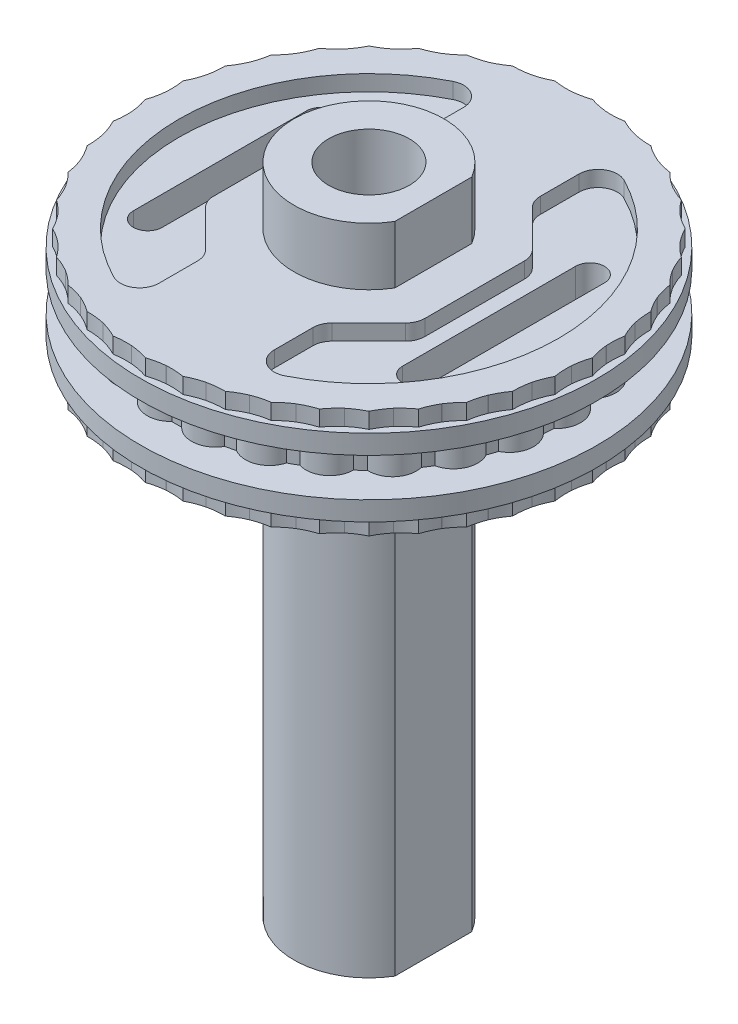
SolidWorks part; units mm, degrees
ref_plane "Front Plane" through (0, 0, 0) normal (0, 0, 1) x (1, 0, 0)
ref_plane "Top Plane" through (0, 0, 0) normal (0, 1, 0) x (1, 0, 0)
ref_plane "Right Plane" through (0, 0, 0) normal (1, 0, 0) x (0, 0, -1)
sketch "Sketch1" plane through (0, 0, 0) normal (1, 0, 0) x (0, 0, -1)
  line L0 (0, -0.599) -> (0, 0.599) construction
  line L1 (-5, -0.5) -> (0, -0.5)
  line L2 (-5, -0.5) -> (-5, 0.5)
  line L3 (-5, 0.5) -> (0, 0.5)
  line L4 (0, -0.5) -> (0, 0.5)
  line L5 (-5, -0.5) -> (0, 0.5) construction
  line L6 (-5, 0.5) -> (0, -0.5) construction
  point P0 (-2.5, 0)
  point P8 (0, 0)
  dimension "D2" = 5
  dimension "D3" = 1
revolve "Revolve1" add sketch "Sketch1" angle 360 about L0
sketch "Sketch2" plane through (0, 0.5, 0) normal (0, 1, 0) x (1, 0, 0)
  line L0 (0, 0) -> (0, 5.2249) construction
  arc A0 (-0.5, 4.9749) -> (0.5, 4.9749) centre (0, 4.5999) cw
  circle A1 centre (0, 0) radius 5 construction
  circle A4 centre (0, 0) radius 5
  arc A5 (0.5, 4.9749) -> (-0.5, 4.9749) centre (0, 0) ccw
  dimension "D1" = 0
  dimension "D2" = 1
  dimension "D3" = 0.25
extrude "Boss-Extrude1" add sketch "Sketch2" against normal up to surface (1 mm away) from surface at 0 up to face at (0, -0.5, -5) starting at face at (0, 0.5, -5)
pattern_circular "CirPattern1" count 25 over 360 about axis through (0, 0, 0) along (0, 1, 0) of "Boss-Extrude1"
sketch "Sketch3" plane through (0, 0, 0) normal (1, 0, 0) x (0, 0, -1)
  line L0 (0, 0) -> (0, 0.5) construction
  line L1 (0, 0.5) -> (-5.9387, 0.5)
  line L3 (-5.7387, 1) -> (-5.9387, 1)
  line L4 (-5.9387, 0.5) -> (-5.9387, 1)
  line L6 (0, 0.5) -> (0, 1.4)
  line L7 (0, 1.4) -> (-5.7387, 1.4)
  line L8 (-5.7387, 1) -> (-5.7387, 1.4)
  line L9 (0.8114, 0.5) -> (-0.1866, 0.5) construction
  line L10 (-5.1887, 0.5) -> (-5.1887, -0.5) construction
  dimension "D1" = 0.5
  dimension "D2" = 0.4
  dimension "D3" = 0.75
  dimension "D4" = 0.2
revolve "Revolve2" add sketch "Sketch3" angle 360 about L0
sketch "Sketch4" plane through (0, 1.4, 0) normal (0, 1, 0) x (1, 0, 0)
  line L0 (0, 0) -> (0, 5.8168) construction
  arc A0 (-0.5, 5.7168) -> (0, 5.8168) centre (-0.639, 7.712) ccw
  arc A1 (0, 5.8168) -> (0.5, 5.7168) centre (0.639, 7.712) ccw
  circle A3 centre (0, 0) radius 5.7387 construction
  circle A4 centre (0, 0) radius 5.7387
  arc A5 (0.5, 5.7168) -> (-0.5, 5.7168) centre (0, 0) ccw
  circle M2 centre (0, 0) radius 5.7387
  dimension "D4" = 2
  dimension "D2" = 0.1
  dimension "D3" = 1
  dimension "D1" = 0
extrude "Boss-Extrude2" add sketch "Sketch4" against normal up to surface (0.4 mm away) contours L0 A1 M2 | A5 L0 A0 up to face at (0, 1, -5.9387)
pattern_circular "CirPattern2" count 40 over 360 about axis through (0, 0, 0) along (0, 1, 0) of "Boss-Extrude2"
mirror "Mirror2" about plane through (0, 0, 0) normal (0, 1, 0) of "Revolve2", "Boss-Extrude2", "CirPattern2"
sketch "Sketch16" plane through (0, 1.4, 0) normal (0, 1, 0) x (1, 0, 0)
  line L80 (-1.3373, 5.5807) -> (-1.3421, 5.5795)
  line L81 (-2.1938, 5.3028) -> (-2.1984, 5.3009)
  line L82 (-2.9963, 4.8943) -> (-3.0006, 4.8917)
  line L83 (-3.7251, 4.3653) -> (-3.7289, 4.3621)
  line L84 (-4.3621, 3.7289) -> (-4.3653, 3.7251)
  line L85 (-4.8917, 3.0006) -> (-4.8943, 2.9963)
  line L86 (-5.3009, 2.1984) -> (-5.3028, 2.1938)
  line L87 (-5.5795, 1.3421) -> (-5.5807, 1.3373)
  line L88 (-5.7208, 0.4527) -> (-5.7212, 0.4478)
  line L89 (-5.7212, -0.4478) -> (-5.7208, -0.4527)
  line L90 (-5.5807, -1.3373) -> (-5.5795, -1.3421)
  line L91 (-5.3028, -2.1938) -> (-5.3009, -2.1984)
  line L92 (-4.8943, -2.9963) -> (-4.8917, -3.0006)
  line L93 (-4.3653, -3.7251) -> (-4.3621, -3.7289)
  line L94 (-3.7289, -4.3621) -> (-3.7251, -4.3653)
  line L95 (-3.0006, -4.8917) -> (-2.9963, -4.8943)
  line L96 (-2.1984, -5.3009) -> (-2.1938, -5.3028)
  line L97 (-1.3421, -5.5795) -> (-1.3373, -5.5807)
  line L98 (-0.4527, -5.7208) -> (-0.4478, -5.7212)
  line L99 (0.4478, -5.7212) -> (0.4527, -5.7208)
  line L100 (1.3373, -5.5807) -> (1.3421, -5.5795)
  line L101 (2.1938, -5.3028) -> (2.1984, -5.3009)
  line L102 (2.9963, -4.8943) -> (3.0006, -4.8917)
  line L103 (3.7251, -4.3653) -> (3.7289, -4.3621)
  line L104 (4.3621, -3.7289) -> (4.3653, -3.7251)
  line L105 (4.8917, -3.0006) -> (4.8943, -2.9963)
  line L106 (5.3009, -2.1984) -> (5.3028, -2.1938)
  line L107 (5.5795, -1.3421) -> (5.5807, -1.3373)
  line L108 (5.7208, -0.4527) -> (5.7212, -0.4478)
  line L109 (5.7212, 0.4478) -> (5.7208, 0.4527)
  line L110 (5.5807, 1.3373) -> (5.5795, 1.3421)
  line L111 (5.3028, 2.1938) -> (5.3009, 2.1984)
  line L112 (4.8943, 2.9963) -> (4.8917, 3.0006)
  line L113 (4.3653, 3.7251) -> (4.3621, 3.7289)
  line L114 (3.7289, 4.3621) -> (3.7251, 4.3653)
  line L115 (3.0006, 4.8917) -> (2.9963, 4.8943)
  line L116 (2.1984, 5.3009) -> (2.1938, 5.3028)
  line L117 (1.3421, 5.5795) -> (1.3373, 5.5807)
  line L118 (0.4527, 5.7208) -> (0.4478, 5.7212)
  line L119 (-0.4478, 5.7212) -> (-0.4527, 5.7208)
  line L120 (-1.3373, 5.5807) -> (-1.3421, 5.5795)
  line L121 (-2.1938, 5.3028) -> (-2.1984, 5.3009)
  line L122 (-2.9963, 4.8943) -> (-3.0006, 4.8917)
  line L123 (-3.7251, 4.3653) -> (-3.7289, 4.3621)
  line L124 (-4.3621, 3.7289) -> (-4.3653, 3.7251)
  line L125 (-4.8917, 3.0006) -> (-4.8943, 2.9963)
  line L126 (-5.3009, 2.1984) -> (-5.3028, 2.1938)
  line L127 (-5.5795, 1.3421) -> (-5.5807, 1.3373)
  line L128 (-5.7208, 0.4527) -> (-5.7212, 0.4478)
  line L129 (-5.7212, -0.4478) -> (-5.7208, -0.4527)
  line L130 (-5.5807, -1.3373) -> (-5.5795, -1.3421)
  line L131 (-5.3028, -2.1938) -> (-5.3009, -2.1984)
  line L132 (-4.8943, -2.9963) -> (-4.8917, -3.0006)
  line L133 (-4.3653, -3.7251) -> (-4.3621, -3.7289)
  line L134 (-3.7289, -4.3621) -> (-3.7251, -4.3653)
  line L135 (-3.0006, -4.8917) -> (-2.9963, -4.8943)
  line L136 (-2.1984, -5.3009) -> (-2.1938, -5.3028)
  line L137 (-1.3421, -5.5795) -> (-1.3373, -5.5807)
  line L138 (-0.4527, -5.7208) -> (-0.4478, -5.7212)
  line L139 (0.4478, -5.7212) -> (0.4527, -5.7208)
  line L140 (1.3373, -5.5807) -> (1.3421, -5.5795)
  line L141 (2.1938, -5.3028) -> (2.1984, -5.3009)
  line L142 (2.9963, -4.8943) -> (3.0006, -4.8917)
  line L143 (3.7251, -4.3653) -> (3.7289, -4.3621)
  line L144 (4.3621, -3.7289) -> (4.3653, -3.7251)
  line L145 (4.8917, -3.0006) -> (4.8943, -2.9963)
  line L146 (5.3009, -2.1984) -> (5.3028, -2.1938)
  line L147 (5.5795, -1.3421) -> (5.5807, -1.3373)
  line L148 (5.7208, -0.4527) -> (5.7212, -0.4478)
  line L149 (5.7212, 0.4478) -> (5.7208, 0.4527)
  line L150 (5.5807, 1.3373) -> (5.5795, 1.3421)
  line L151 (5.3028, 2.1938) -> (5.3009, 2.1984)
  line L152 (4.8943, 2.9963) -> (4.8917, 3.0006)
  line L153 (4.3653, 3.7251) -> (4.3621, 3.7289)
  line L154 (3.7289, 4.3621) -> (3.7251, 4.3653)
  line L155 (3.0006, 4.8917) -> (2.9963, 4.8943)
  line L156 (2.1984, 5.3009) -> (2.1938, 5.3028)
  line L157 (1.3421, 5.5795) -> (1.3373, 5.5807)
  line L158 (0.4527, 5.7208) -> (0.4478, 5.7212)
  line L159 (-0.4478, 5.7212) -> (-0.4527, 5.7208)
  arc A160 (-1.7975, 5.5321) -> (-1.3421, 5.5795) centre (-1.7754, 7.532) ccw
  arc A161 (-2.1938, 5.3028) -> (-1.7975, 5.5321) centre (-2.9909, 7.1371) ccw
  arc A162 (-2.6408, 5.1828) -> (-2.1984, 5.3009) centre (-2.9318, 7.1616) ccw
  arc A163 (-2.9963, 4.8943) -> (-2.6408, 5.1828) centre (-4.0706, 6.5813) ccw
  arc A164 (-3.4191, 4.7059) -> (-3.0006, 4.8917) centre (-4.016, 6.6148) ccw
  arc A165 (-3.7251, 4.3653) -> (-3.4191, 4.7059) centre (-5.05, 5.8635) ccw
  arc A166 (-4.1131, 4.1131) -> (-3.7289, 4.3621) centre (-5.0013, 5.9051) ccw
  arc A167 (-4.3621, 3.7289) -> (-4.1131, 4.1131) centre (-5.9051, 5.0013) ccw
  arc A168 (-4.7059, 3.4191) -> (-4.3653, 3.7251) centre (-5.8635, 5.05) ccw
  arc A169 (-4.8917, 3.0006) -> (-4.7059, 3.4191) centre (-6.6148, 4.016) ccw
  arc A170 (-5.1828, 2.6408) -> (-4.8943, 2.9963) centre (-6.5813, 4.0706) ccw
  arc A171 (-5.3009, 2.1984) -> (-5.1828, 2.6408) centre (-7.1616, 2.9318) ccw
  arc A172 (-5.5321, 1.7975) -> (-5.3028, 2.1938) centre (-7.1371, 2.9909) ccw
  arc A173 (-5.5795, 1.3421) -> (-5.5321, 1.7975) centre (-7.532, 1.7754) ccw
  arc A174 (-5.7452, 0.91) -> (-5.5807, 1.3373) centre (-7.5171, 1.8376) ccw
  arc A175 (-5.7208, 0.4527) -> (-5.7452, 0.91) centre (-7.717, 0.5753) ccw
  arc A176 (-5.8168, 0) -> (-5.7212, 0.4478) centre (-7.712, 0.639) ccw
  arc A177 (-5.7212, -0.4478) -> (-5.8168, 0) centre (-7.712, -0.639) ccw
  arc A178 (-5.7452, -0.91) -> (-5.7208, -0.4527) centre (-7.717, -0.5753) ccw
  arc A179 (-5.5807, -1.3373) -> (-5.7452, -0.91) centre (-7.5171, -1.8376) ccw
  arc A180 (-5.5321, -1.7975) -> (-5.5795, -1.3421) centre (-7.532, -1.7754) ccw
  arc A181 (-5.3028, -2.1938) -> (-5.5321, -1.7975) centre (-7.1371, -2.9909) ccw
  arc A182 (-5.1828, -2.6408) -> (-5.3009, -2.1984) centre (-7.1616, -2.9318) ccw
  arc A183 (-4.8943, -2.9963) -> (-5.1828, -2.6408) centre (-6.5813, -4.0706) ccw
  arc A184 (-4.7059, -3.4191) -> (-4.8917, -3.0006) centre (-6.6148, -4.016) ccw
  arc A185 (-4.3653, -3.7251) -> (-4.7059, -3.4191) centre (-5.8635, -5.05) ccw
  arc A186 (-4.1131, -4.1131) -> (-4.3621, -3.7289) centre (-5.9051, -5.0013) ccw
  arc A187 (-3.7289, -4.3621) -> (-4.1131, -4.1131) centre (-5.0013, -5.9051) ccw
  arc A188 (-3.4191, -4.7059) -> (-3.7251, -4.3653) centre (-5.05, -5.8635) ccw
  arc A189 (-3.0006, -4.8917) -> (-3.4191, -4.7059) centre (-4.016, -6.6148) ccw
  arc A190 (-2.6408, -5.1828) -> (-2.9963, -4.8943) centre (-4.0706, -6.5813) ccw
  arc A191 (-2.1984, -5.3009) -> (-2.6408, -5.1828) centre (-2.9318, -7.1616) ccw
  arc A192 (-1.7975, -5.5321) -> (-2.1938, -5.3028) centre (-2.9909, -7.1371) ccw
  arc A193 (-1.3421, -5.5795) -> (-1.7975, -5.5321) centre (-1.7754, -7.532) ccw
  arc A194 (-0.91, -5.7452) -> (-1.3373, -5.5807) centre (-1.8376, -7.5171) ccw
  arc A195 (-0.4527, -5.7208) -> (-0.91, -5.7452) centre (-0.5753, -7.717) ccw
  arc A196 (0, -5.8168) -> (-0.4478, -5.7212) centre (-0.639, -7.712) ccw
  arc A197 (0.4478, -5.7212) -> (0, -5.8168) centre (0.639, -7.712) ccw
  arc A198 (0.91, -5.7452) -> (0.4527, -5.7208) centre (0.5753, -7.717) ccw
  arc A199 (1.3373, -5.5807) -> (0.91, -5.7452) centre (1.8376, -7.5171) ccw
  arc A200 (1.7975, -5.5321) -> (1.3421, -5.5795) centre (1.7754, -7.532) ccw
  arc A201 (2.1938, -5.3028) -> (1.7975, -5.5321) centre (2.9909, -7.1371) ccw
  arc A202 (2.6408, -5.1828) -> (2.1984, -5.3009) centre (2.9318, -7.1616) ccw
  arc A203 (2.9963, -4.8943) -> (2.6408, -5.1828) centre (4.0706, -6.5813) ccw
  arc A204 (3.4191, -4.7059) -> (3.0006, -4.8917) centre (4.016, -6.6148) ccw
  arc A205 (3.7251, -4.3653) -> (3.4191, -4.7059) centre (5.05, -5.8635) ccw
  arc A206 (4.1131, -4.1131) -> (3.7289, -4.3621) centre (5.0013, -5.9051) ccw
  arc A207 (4.3621, -3.7289) -> (4.1131, -4.1131) centre (5.9051, -5.0013) ccw
  arc A208 (4.7059, -3.4191) -> (4.3653, -3.7251) centre (5.8635, -5.05) ccw
  arc A209 (4.8917, -3.0006) -> (4.7059, -3.4191) centre (6.6148, -4.016) ccw
  arc A210 (5.1828, -2.6408) -> (4.8943, -2.9963) centre (6.5813, -4.0706) ccw
  arc A211 (5.3009, -2.1984) -> (5.1828, -2.6408) centre (7.1616, -2.9318) ccw
  arc A212 (5.5321, -1.7975) -> (5.3028, -2.1938) centre (7.1371, -2.9909) ccw
  arc A213 (5.5795, -1.3421) -> (5.5321, -1.7975) centre (7.532, -1.7754) ccw
  arc A214 (5.7452, -0.91) -> (5.5807, -1.3373) centre (7.5171, -1.8376) ccw
  arc A215 (5.7208, -0.4527) -> (5.7452, -0.91) centre (7.717, -0.5753) ccw
  arc A216 (5.8168, 0) -> (5.7212, -0.4478) centre (7.712, -0.639) ccw
  arc A217 (5.7212, 0.4478) -> (5.8168, 0) centre (7.712, 0.639) ccw
  arc A218 (5.7452, 0.91) -> (5.7208, 0.4527) centre (7.717, 0.5753) ccw
  arc A219 (5.5807, 1.3373) -> (5.7452, 0.91) centre (7.5171, 1.8376) ccw
  arc A220 (5.5321, 1.7975) -> (5.5795, 1.3421) centre (7.532, 1.7754) ccw
  arc A221 (5.3028, 2.1938) -> (5.5321, 1.7975) centre (7.1371, 2.9909) ccw
  arc A222 (5.1828, 2.6408) -> (5.3009, 2.1984) centre (7.1616, 2.9318) ccw
  arc A223 (4.8943, 2.9963) -> (5.1828, 2.6408) centre (6.5813, 4.0706) ccw
  arc A224 (4.7059, 3.4191) -> (4.8917, 3.0006) centre (6.6148, 4.016) ccw
  arc A225 (4.3653, 3.7251) -> (4.7059, 3.4191) centre (5.8635, 5.05) ccw
  arc A226 (4.1131, 4.1131) -> (4.3621, 3.7289) centre (5.9051, 5.0013) ccw
  arc A227 (3.7289, 4.3621) -> (4.1131, 4.1131) centre (5.0013, 5.9051) ccw
  arc A228 (3.4191, 4.7059) -> (3.7251, 4.3653) centre (5.05, 5.8635) ccw
  arc A229 (3.0006, 4.8917) -> (3.4191, 4.7059) centre (4.016, 6.6148) ccw
  arc A230 (2.6408, 5.1828) -> (2.9963, 4.8943) centre (4.0706, 6.5813) ccw
  arc A231 (2.1984, 5.3009) -> (2.6408, 5.1828) centre (2.9318, 7.1616) ccw
  arc A232 (1.7975, 5.5321) -> (2.1938, 5.3028) centre (2.9909, 7.1371) ccw
  arc A233 (1.3421, 5.5795) -> (1.7975, 5.5321) centre (1.7754, 7.532) ccw
  arc A234 (0.91, 5.7452) -> (1.3373, 5.5807) centre (1.8376, 7.5171) ccw
  arc A235 (0.4527, 5.7208) -> (0.91, 5.7452) centre (0.5753, 7.717) ccw
  arc A236 (0, 5.8168) -> (0.4478, 5.7212) centre (0.639, 7.712) ccw
  arc A237 (-0.4478, 5.7212) -> (0, 5.8168) centre (-0.639, 7.712) ccw
  arc A238 (-0.91, 5.7452) -> (-0.4527, 5.7208) centre (-0.5753, 7.717) ccw
  arc A239 (-1.3373, 5.5807) -> (-0.91, 5.7452) centre (-1.8376, 7.5171) ccw
  arc A240 (-1.7975, 5.5321) -> (-1.3421, 5.5795) centre (-1.7754, 7.532) ccw
  arc A241 (-2.1938, 5.3028) -> (-1.7975, 5.5321) centre (-2.9909, 7.1371) ccw
  arc A242 (-2.6408, 5.1828) -> (-2.1984, 5.3009) centre (-2.9318, 7.1616) ccw
  arc A243 (-2.9963, 4.8943) -> (-2.6408, 5.1828) centre (-4.0706, 6.5813) ccw
  arc A244 (-3.4191, 4.7059) -> (-3.0006, 4.8917) centre (-4.016, 6.6148) ccw
  arc A245 (-3.7251, 4.3653) -> (-3.4191, 4.7059) centre (-5.05, 5.8635) ccw
  arc A246 (-4.1131, 4.1131) -> (-3.7289, 4.3621) centre (-5.0013, 5.9051) ccw
  arc A247 (-4.3621, 3.7289) -> (-4.1131, 4.1131) centre (-5.9051, 5.0013) ccw
  arc A248 (-4.7059, 3.4191) -> (-4.3653, 3.7251) centre (-5.8635, 5.05) ccw
  arc A249 (-4.8917, 3.0006) -> (-4.7059, 3.4191) centre (-6.6148, 4.016) ccw
  arc A250 (-5.1828, 2.6408) -> (-4.8943, 2.9963) centre (-6.5813, 4.0706) ccw
  arc A251 (-5.3009, 2.1984) -> (-5.1828, 2.6408) centre (-7.1616, 2.9318) ccw
  arc A252 (-5.5321, 1.7975) -> (-5.3028, 2.1938) centre (-7.1371, 2.9909) ccw
  arc A253 (-5.5795, 1.3421) -> (-5.5321, 1.7975) centre (-7.532, 1.7754) ccw
  arc A254 (-5.7452, 0.91) -> (-5.5807, 1.3373) centre (-7.5171, 1.8376) ccw
  arc A255 (-5.7208, 0.4527) -> (-5.7452, 0.91) centre (-7.717, 0.5753) ccw
  arc A256 (-5.8168, 0) -> (-5.7212, 0.4478) centre (-7.712, 0.639) ccw
  arc A257 (-5.7212, -0.4478) -> (-5.8168, 0) centre (-7.712, -0.639) ccw
  arc A258 (-5.7452, -0.91) -> (-5.7208, -0.4527) centre (-7.717, -0.5753) ccw
  arc A259 (-5.5807, -1.3373) -> (-5.7452, -0.91) centre (-7.5171, -1.8376) ccw
  arc A260 (-5.5321, -1.7975) -> (-5.5795, -1.3421) centre (-7.532, -1.7754) ccw
  arc A261 (-5.3028, -2.1938) -> (-5.5321, -1.7975) centre (-7.1371, -2.9909) ccw
  arc A262 (-5.1828, -2.6408) -> (-5.3009, -2.1984) centre (-7.1616, -2.9318) ccw
  arc A263 (-4.8943, -2.9963) -> (-5.1828, -2.6408) centre (-6.5813, -4.0706) ccw
  arc A264 (-4.7059, -3.4191) -> (-4.8917, -3.0006) centre (-6.6148, -4.016) ccw
  arc A265 (-4.3653, -3.7251) -> (-4.7059, -3.4191) centre (-5.8635, -5.05) ccw
  arc A266 (-4.1131, -4.1131) -> (-4.3621, -3.7289) centre (-5.9051, -5.0013) ccw
  arc A267 (-3.7289, -4.3621) -> (-4.1131, -4.1131) centre (-5.0013, -5.9051) ccw
  arc A268 (-3.4191, -4.7059) -> (-3.7251, -4.3653) centre (-5.05, -5.8635) ccw
  arc A269 (-3.0006, -4.8917) -> (-3.4191, -4.7059) centre (-4.016, -6.6148) ccw
  arc A270 (-2.6408, -5.1828) -> (-2.9963, -4.8943) centre (-4.0706, -6.5813) ccw
  arc A271 (-2.1984, -5.3009) -> (-2.6408, -5.1828) centre (-2.9318, -7.1616) ccw
  arc A272 (-1.7975, -5.5321) -> (-2.1938, -5.3028) centre (-2.9909, -7.1371) ccw
  arc A273 (-1.3421, -5.5795) -> (-1.7975, -5.5321) centre (-1.7754, -7.532) ccw
  arc A274 (-0.91, -5.7452) -> (-1.3373, -5.5807) centre (-1.8376, -7.5171) ccw
  arc A275 (-0.4527, -5.7208) -> (-0.91, -5.7452) centre (-0.5753, -7.717) ccw
  arc A276 (0, -5.8168) -> (-0.4478, -5.7212) centre (-0.639, -7.712) ccw
  arc A277 (0.4478, -5.7212) -> (0, -5.8168) centre (0.639, -7.712) ccw
  arc A278 (0.91, -5.7452) -> (0.4527, -5.7208) centre (0.5753, -7.717) ccw
  arc A279 (1.3373, -5.5807) -> (0.91, -5.7452) centre (1.8376, -7.5171) ccw
  arc A280 (1.7975, -5.5321) -> (1.3421, -5.5795) centre (1.7754, -7.532) ccw
  arc A281 (2.1938, -5.3028) -> (1.7975, -5.5321) centre (2.9909, -7.1371) ccw
  arc A282 (2.6408, -5.1828) -> (2.1984, -5.3009) centre (2.9318, -7.1616) ccw
  arc A283 (2.9963, -4.8943) -> (2.6408, -5.1828) centre (4.0706, -6.5813) ccw
  arc A284 (3.4191, -4.7059) -> (3.0006, -4.8917) centre (4.016, -6.6148) ccw
  arc A285 (3.7251, -4.3653) -> (3.4191, -4.7059) centre (5.05, -5.8635) ccw
  arc A286 (4.1131, -4.1131) -> (3.7289, -4.3621) centre (5.0013, -5.9051) ccw
  arc A287 (4.3621, -3.7289) -> (4.1131, -4.1131) centre (5.9051, -5.0013) ccw
  arc A288 (4.7059, -3.4191) -> (4.3653, -3.7251) centre (5.8635, -5.05) ccw
  arc A289 (4.8917, -3.0006) -> (4.7059, -3.4191) centre (6.6148, -4.016) ccw
  arc A290 (5.1828, -2.6408) -> (4.8943, -2.9963) centre (6.5813, -4.0706) ccw
  arc A291 (5.3009, -2.1984) -> (5.1828, -2.6408) centre (7.1616, -2.9318) ccw
  arc A292 (5.5321, -1.7975) -> (5.3028, -2.1938) centre (7.1371, -2.9909) ccw
  arc A293 (5.5795, -1.3421) -> (5.5321, -1.7975) centre (7.532, -1.7754) ccw
  arc A294 (5.7452, -0.91) -> (5.5807, -1.3373) centre (7.5171, -1.8376) ccw
  arc A295 (5.7208, -0.4527) -> (5.7452, -0.91) centre (7.717, -0.5753) ccw
  arc A296 (5.8168, 0) -> (5.7212, -0.4478) centre (7.712, -0.639) ccw
  arc A297 (5.7212, 0.4478) -> (5.8168, 0) centre (7.712, 0.639) ccw
  arc A298 (5.7452, 0.91) -> (5.7208, 0.4527) centre (7.717, 0.5753) ccw
  arc A299 (5.5807, 1.3373) -> (5.7452, 0.91) centre (7.5171, 1.8376) ccw
  arc A300 (5.5321, 1.7975) -> (5.5795, 1.3421) centre (7.532, 1.7754) ccw
  arc A301 (5.3028, 2.1938) -> (5.5321, 1.7975) centre (7.1371, 2.9909) ccw
  arc A302 (5.1828, 2.6408) -> (5.3009, 2.1984) centre (7.1616, 2.9318) ccw
  arc A303 (4.8943, 2.9963) -> (5.1828, 2.6408) centre (6.5813, 4.0706) ccw
  arc A304 (4.7059, 3.4191) -> (4.8917, 3.0006) centre (6.6148, 4.016) ccw
  arc A305 (4.3653, 3.7251) -> (4.7059, 3.4191) centre (5.8635, 5.05) ccw
  arc A306 (4.1131, 4.1131) -> (4.3621, 3.7289) centre (5.9051, 5.0013) ccw
  arc A307 (3.7289, 4.3621) -> (4.1131, 4.1131) centre (5.0013, 5.9051) ccw
  arc A308 (3.4191, 4.7059) -> (3.7251, 4.3653) centre (5.05, 5.8635) ccw
  arc A309 (3.0006, 4.8917) -> (3.4191, 4.7059) centre (4.016, 6.6148) ccw
  arc A310 (2.6408, 5.1828) -> (2.9963, 4.8943) centre (4.0706, 6.5813) ccw
  arc A311 (2.1984, 5.3009) -> (2.6408, 5.1828) centre (2.9318, 7.1616) ccw
  arc A312 (1.7975, 5.5321) -> (2.1938, 5.3028) centre (2.9909, 7.1371) ccw
  arc A313 (1.3421, 5.5795) -> (1.7975, 5.5321) centre (1.7754, 7.532) ccw
  arc A314 (0.91, 5.7452) -> (1.3373, 5.5807) centre (1.8376, 7.5171) ccw
  arc A315 (0.4527, 5.7208) -> (0.91, 5.7452) centre (0.5753, 7.717) ccw
  arc A316 (0, 5.8168) -> (0.4478, 5.7212) centre (0.639, 7.712) ccw
  arc A317 (-0.4478, 5.7212) -> (0, 5.8168) centre (-0.639, 7.712) ccw
  arc A318 (-0.91, 5.7452) -> (-0.4527, 5.7208) centre (-0.5753, 7.717) ccw
  arc A319 (-1.3373, 5.5807) -> (-0.91, 5.7452) centre (-1.8376, 7.5171) ccw
  dimension "D1" = 0
extrude "Boss-Extrude4" add sketch "Sketch16" along normal blind 0.01
sketch "Sketch5" plane through (0, 1.41, 0) normal (0, 1, 0) x (1, 0, 0)
  line L0 (1.6741, 1) -> (1.6741, -1)
  arc A0 (1.6741, 1) -> (1.6741, -1) centre (0, 0) ccw
  point P5 (1.6741, 0)
  dimension "D1" = 3.9
  dimension "D2" = 2
extrude "Boss-Extrude3" add sketch "Sketch5" against normal blind 17 from offset 1.5
sketch "Sketch7" plane through (0, 0, 0) normal (0, -1, 0) x (1, 0, 0)
  line L0 (-3.5, -2.25) -> (-3.5, 2.25) construction
  line L1 (-3.875, -2.25) -> (-3.875, 2.25)
  line L2 (-3.125, -2.25) -> (-3.125, 2.25)
  line L3 (0, 0) -> (0, 3.3928) construction
  line L4 (3.5, -2.25) -> (3.5, 2.25) construction
  line L5 (3.875, -2.25) -> (3.875, 2.25)
  line L6 (3.125, -2.25) -> (3.125, 2.25)
  arc A0 (-3.875, -2.25) -> (-3.125, -2.25) centre (-3.5, -2.25) ccw
  arc A1 (-3.125, 2.25) -> (-3.875, 2.25) centre (-3.5, 2.25) ccw
  arc A2 (3.875, -2.25) -> (3.125, -2.25) centre (3.5, -2.25) cw
  arc A3 (3.125, 2.25) -> (3.875, 2.25) centre (3.5, 2.25) cw
  point P2 (-3.5, 0)
  point P14 (3.5, 0)
  dimension "D1" = 3.5
  dimension "D2" = 0.75
  dimension "D3" = 4.5
extrude "Cut-Extrude2" cut sketch "Sketch7" against normal through all both and the other way through all
sketch "Sketch9" plane through (0, 1.41, 0) normal (0, 1, 0) x (1, 0, 0)
  line L0 (-1.5, 3.9625) -> (-1.5, 2.9571)
  line L1 (0, 0) -> (-1.5, 0) construction
  line L2 (-2.75, -1.2929) -> (-2.75, 1.2929)
  line L3 (-2.6036, 1.6464) -> (-1.6464, 2.6036)
  line L4 (-2.6036, -1.6464) -> (-1.6464, -2.6036)
  line L5 (-1.5, 0) -> (-2.75, 0) construction
  line L6 (-1.5, -2.9571) -> (-1.5, -3.9625)
  arc A0 (-1.5, -3.9625) -> (-2.2253, -4.4089) centre (-2, -3.9625) cw
  arc A1 (-1.5, 3.9625) -> (-2.2253, 4.4089) centre (-2, 3.9625) ccw
  circle A2 centre (0, 0) radius 4.9387
  arc A3 (-2.2253, 4.4089) -> (-2.2253, -4.4089) centre (0, 0) ccw
  arc A4 (-1.5, 2.9571) -> (-1.6464, 2.6036) centre (-2, 2.9571) cw
  arc A5 (-1.6464, -2.6036) -> (-1.5, -2.9571) centre (-2, -2.9571) cw
  arc A6 (-2.75, 1.2929) -> (-2.6036, 1.6464) centre (-2.25, 1.2929) cw
  arc A7 (-2.6036, -1.6464) -> (-2.75, -1.2929) centre (-2.25, -1.2929) cw
  point P18 (-1.5, 2.75)
  point P21 (-1.5, -2.75)
  point P24 (-2.75, 1.5)
  point P27 (-2.75, -1.5)
  dimension "D6" = 0.5
  dimension "D2" = 1.5
  dimension "D3" = 1.25
  dimension "D4" = 3
  dimension "D5" = 45
  dimension "D1" = 1
extrude "Cut-Extrude3" cut sketch "Sketch9" against normal up to surface (0.41 mm away) up to face at (0, 1, -5.9387)
mirror "Mirror3" about plane through (0, 0, 0) normal (1, 0, 0) of "Cut-Extrude3"
sketch "Sketch12" plane through (0, 2.91, 0) normal (0, 1, 0) x (1, 0, 0)
  circle A0 centre (0, 0) radius 5.9387 construction
  point P0 (0, 0)
hole_wizard "Ø2.0mm Dowel Hole1" positions "Sketch12" profile "Sketch11" hole size "Ø2.0" standard "ANSI Metric"
sketch "Sketch11" plane through (0, 2.91, 0) normal (1, 0, 0) x (0, 0, 1)
  line L0 (0, 0) -> (0, 8)
  line L1 (0, 8) -> (1.05, 7.3691)
  line L2 (1.05, 7.3691) -> (1.05, 0)
  line L5 (1.05, 0) -> (0, 0)
  line L10 (0, 8) -> (-1.05, 7.3691) construction
  line L11 (0, -6.35) -> (0, 107.95) construction
  dimension "Hole Dia." = 2.1
  dimension "Hole Depth" = 8
  dimension "Drill Angle" = 118
sketch "Sketch15" plane through (0, -14.09, 0) normal (0, -1, 0) x (-1, 0, 0)
  point P0 (0, 0)
hole_wizard "Ø2.0mm Dowel Hole2" positions "Sketch15" profile "Sketch14" hole size "Ø2.0" standard "ANSI Metric"
sketch "Sketch14" plane through (0, -14.09, 0) normal (1, 0, 0) x (0, 0, -1)
  line L0 (0, 0) -> (0, 8)
  line L1 (0, 8) -> (1.05, 7.3691)
  line L2 (1.05, 7.3691) -> (1.05, 0)
  line L5 (1.05, 0) -> (0, 0)
  line L10 (0, 8) -> (-1.05, 7.3691) construction
  line L11 (0, -6.35) -> (0, 107.95) construction
  dimension "Hole Dia." = 2.1
  dimension "Hole Depth" = 8
  dimension "Drill Angle" = 118
